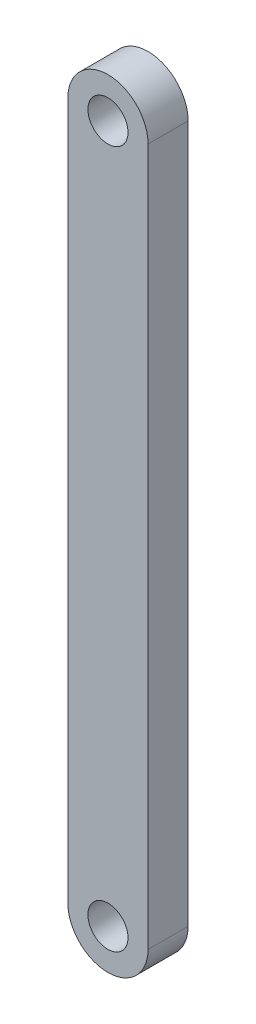
SolidWorks part; units mm, degrees
ref_plane "Front Plane" through (0, 0, 0) normal (0, 0, 1) x (1, 0, 0)
ref_plane "Top Plane" through (0, 0, 0) normal (0, 1, 0) x (1, 0, 0)
ref_plane "Right Plane" through (0, 0, 0) normal (1, 0, 0) x (0, 0, -1)
sketch "Sketch1" plane through (0, 0, 0) normal (0, 0, 1) x (1, 0, 0)
  line L0 (0, 0) -> (0, 110.49) construction
  line L1 (-6.35, 110.49) -> (-6.35, 0)
  line L2 (6.35, 110.49) -> (6.35, 0)
  arc A0 (-6.35, 0) -> (6.35, 0) centre (0, 0) ccw
  arc A1 (6.35, 110.49) -> (-6.35, 110.49) centre (0, 110.49) ccw
  circle A2 centre (0, 110.49) radius 3.175
  circle A3 centre (0, 0) radius 3.175
  dimension "D1" = 6.35
  dimension "D2" = 12.7
  dimension "4.35" = 110.49
extrude "Boss-Extrude1" add sketch "Sketch1" along normal blind 6.35
